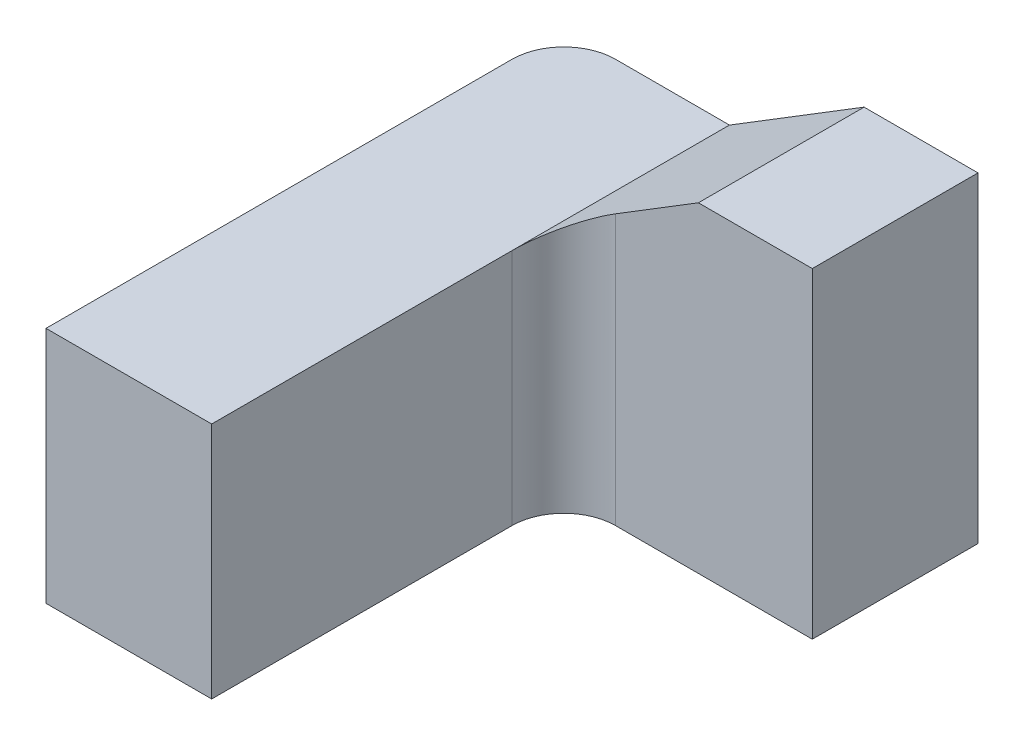
SolidWorks part; units mm, degrees
ref_plane "前视基准面" through (0, 0, 0) normal (0, 0, 1) x (1, 0, 0)
ref_plane "上视基准面" through (0, 0, 0) normal (0, 1, 0) x (1, 0, 0)
ref_plane "右视基准面" through (0, 0, 0) normal (1, 0, 0) x (0, 0, -1)
sketch "草图1" plane through (0, 0, 0) normal (0, 0, 1) x (1, 0, 0)
  line L0 (0, 0) -> (0, 0.23)
  line L1 (0, 0) -> (0.4, 0)
  line L2 (0.4, 0) -> (0.4, 0.31)
  line L3 (0.4, 0.31) -> (0.29, 0.31)
  line L4 (0, 0.23) -> (0.16, 0.23)
  line L5 (0.16, 0.23) -> (0.29, 0.31)
  dimension "D1" = 0.31
  dimension "D2" = 0.23
  dimension "D3" = 0.4
  dimension "D4" = 0.11
  dimension "D5" = 0.16
extrude "凸台-拉伸1" add sketch "草图1" along normal blind 0.16 contours L4 L5 L3 L2 L1 L0
sketch "草图2" plane through (0, 0, 0.16) normal (0, 0, 1) x (1, 0, 0)
  line L0 (0.16, 0.23) -> (0.16, 0) construction
  line L1 (0, 0) -> (0.4, 0) construction
  line L3 (0.16, 0) -> (0, 0)
  line L4 (0.16, 0) -> (0.16, 0.23)
  line L5 (0.16, 0.23) -> (0, 0.23)
  line L6 (0, 0) -> (0, 0.23)
extrude "凸台-拉伸2" add sketch "草图2" along normal blind 0.34
fillet "圆角1" radius 0.05 2 edges at (0, 0.115, 0) (0.16, 0.115, 0.16)
